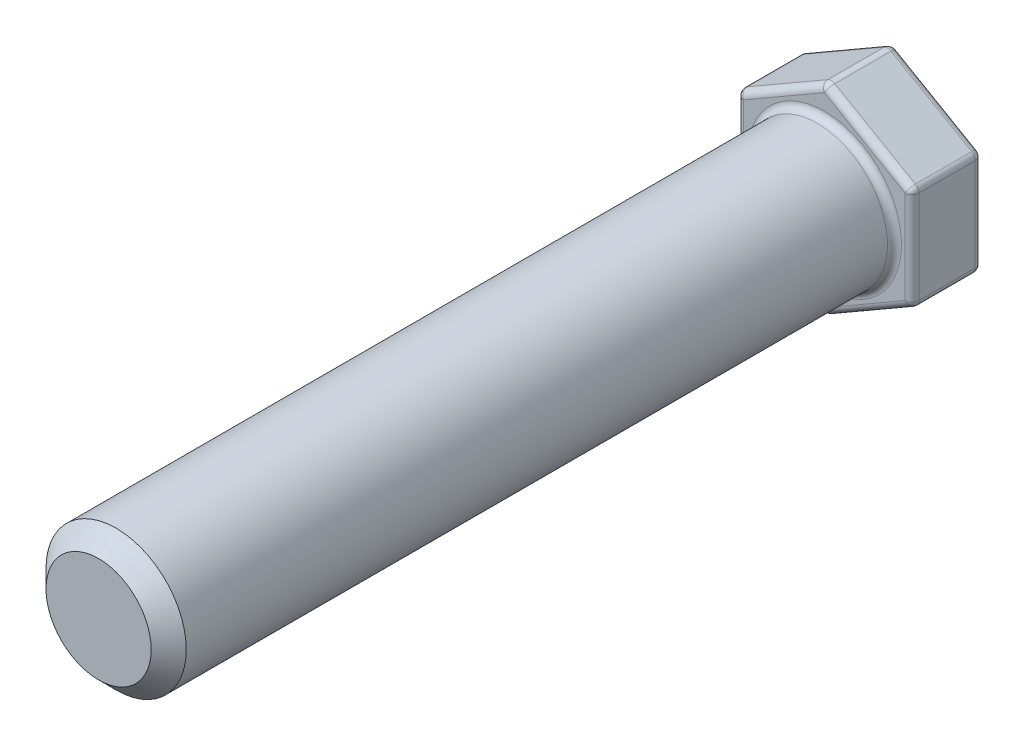
SolidWorks part; units mm, degrees
ref_plane "Front Plane" through (0, 0, 0) normal (0, 0, 1) x (1, 0, 0)
ref_plane "Top Plane" through (0, 0, 0) normal (0, 1, 0) x (1, 0, 0)
ref_plane "Right Plane" through (0, 0, 0) normal (1, 0, 0) x (0, 0, -1)
sketch "Sketch1" plane through (0, 0, 0) normal (0, 0, 1) x (1, 0, 0)
  circle A0 centre (0, 0) radius 2
  dimension "D1" = 4
extrude "Boss-Extrude1" add sketch "Sketch1" along normal blind 20.7
sketch "Sketch2" plane through (0, 0, 0) normal (0, 0, -1) x (-1, 0, 0)
  line L1 (-2.5, 1.4434) -> (-2.5, -1.4434)
  line L2 (-2.5, -1.4434) -> (0, -2.8868)
  line L3 (0, -2.8868) -> (2.5, -1.4434)
  line L4 (2.5, -1.4434) -> (2.5, 1.4434)
  line L5 (2.5, 1.4434) -> (0, 2.8868)
  line L6 (0, 2.8868) -> (-2.5, 1.4434)
  circle A0 centre (0, 0) radius 2.5 construction
  dimension "D1" = 5
extrude "Boss-Extrude2" add sketch "Sketch2" along normal blind 2
fillet "Fillet1" radius 0.2 13 edges at (-1.25, 2.1651, -2) (-2.5, 0, -2) (-1.25, -2.1651, -2) (1.25, -2.1651, -2) (2.5, 0, -2) (1.25, 2.1651, -2) (2.5, 0, 0) (1.25, -2.1651, 0) (-1.25, -2.1651, 0) (-2.5, 0, 0) (-1.25, 2.1651, 0) (1.25, 2.1651, 0) (2, 0, 0)
fillet "Fillet2" radius 0.2 18 edges at (0, 2.8191, -1.9414) (0, 2.8191, -0.0586) (-2.4414, 1.4096, -1.9414) (-2.4414, 1.4096, -0.0586) (-2.4414, -1.4096, -1.9414) (-2.4414, -1.4096, -0.0586) (0, -2.8191, -1.9414) (0, -2.8191, -0.0586) (2.4414, -1.4096, -1.9414) (2.4414, -1.4096, -0.0586) (2.4414, 1.4096, -1.9414) (2.4414, 1.4096, -0.0586) (0, 2.8868, -1) (-2.5, 1.4434, -1) (-2.5, -1.4434, -1) (0, -2.8868, -1) (2.5, -1.4434, -1) (2.5, 1.4434, -1)
chamfer "Chamfer1" distance 0.5 angle 45 1 edges at (2, 0, 20.7)
